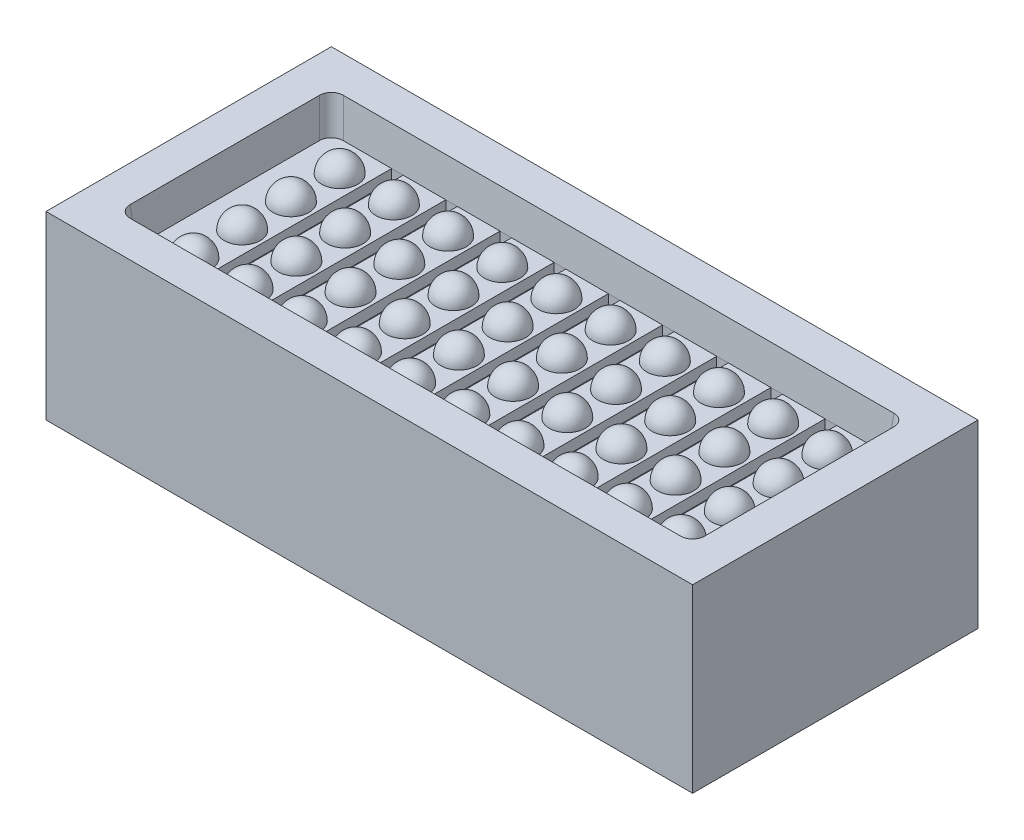
SolidWorks part; units mm, degrees
ref_plane "Front Plane" through (0, 0, 0) normal (0, 0, 1) x (1, 0, 0)
ref_plane "Top Plane" through (0, 0, 0) normal (0, 1, 0) x (1, 0, 0)
ref_plane "Right Plane" through (0, 0, 0) normal (1, 0, 0) x (0, 0, -1)
sketch "Sketch1" plane through (0, 0, 0) normal (0, 1, 0) x (1, 0, 0)
  line L1 (0, 0) -> (-179, 0)
  line L2 (0, 0) -> (0, 79)
  line L3 (0, 79) -> (-179, 79)
  line L4 (-179, 0) -> (-179, 79)
  dimension "D1" = 179
  dimension "D2" = 79
extrude "Boss-Extrude2" add sketch "Sketch1" along normal blind 50
sketch "Sketch2" plane through (0, 50, 0) normal (0, 1, 0) x (1, 0, 0)
  line L0 (0, 79) -> (-179, 79) construction
  line L1 (-169, 69) -> (-10, 69)
  line L2 (-169, 69) -> (-169, 10)
  line L3 (-169, 10) -> (-10, 10)
  line L4 (-10, 69) -> (-10, 10)
  line L5 (-179, 79) -> (-179, 0) construction
  line L6 (0, 0) -> (0, 79) construction
  line L7 (-179, 0) -> (0, 0) construction
  dimension "D1" = 10
  dimension "D2" = 10
  dimension "D3" = 10
  dimension "D4" = 10
extrude "Cut-Extrude1" cut sketch "Sketch2" against normal blind 10 draft 5
fillet "Fillet1" radius 3.3 4 edges at (-10.4374, 45, -10.4374) (-168.5626, 45, -10.4374) (-10.4374, 45, -68.5626) (-168.5626, 45, -68.5626)
sketch "Sketch3" plane through (0, 40, 0) normal (0, 1, 0) x (1, 0, 0)
  line L0 (-157.3488, 64.653) -> (-157.3488, 54.653)
  arc A0 (-157.3488, 54.653) -> (-157.3488, 64.653) centre (-157.3488, 59.653) ccw
  dimension "D1" = 10
revolve "Revolve2" add sketch "Sketch3" angle 360 about L0
pattern_linear "LPattern1" count 10 spacing 15 along (1, 0, 0) of "Revolve2"
pattern_linear "LPattern2" count 4 spacing 13.5 along (0, 0, 1) of "LPattern1", "Revolve2"
sketch "Sketch5" plane through (0, 40, 0) normal (0, 1, 0) x (1, 0, 0)
  line L0 (-152.3488, 59.653) -> (-151.4488, 59.653)
  line L1 (-14.1623, 68.1251) -> (-164.8377, 68.1251) construction
  line L2 (-133.2488, 68.1251) -> (-133.2488, 10.8749)
  line L3 (-164.8377, 10.8749) -> (-14.1623, 10.8749) construction
  line L4 (-148.2488, 68.1251) -> (-151.4488, 68.1251)
  line L5 (-148.2488, 68.1251) -> (-148.2488, 10.8749)
  line L6 (-148.2488, 10.8749) -> (-151.4488, 10.8749)
  line L7 (-151.4488, 68.1251) -> (-151.4488, 10.8749)
  line L8 (-148.2488, 59.653) -> (-147.3488, 59.653)
  line L9 (-136.4488, 68.1251) -> (-136.4488, 10.8749)
  line L10 (-133.2488, 68.1251) -> (-136.4488, 68.1251)
  line L11 (-133.2488, 10.8749) -> (-136.4488, 10.8749)
  line L12 (-118.2488, 68.1251) -> (-118.2488, 10.8749)
  line L13 (-121.4488, 68.1251) -> (-121.4488, 10.8749)
  line L14 (-118.2488, 68.1251) -> (-121.4488, 68.1251)
  line L15 (-118.2488, 10.8749) -> (-121.4488, 10.8749)
  line L16 (-103.2488, 68.1251) -> (-103.2488, 10.8749)
  line L17 (-106.4488, 68.1251) -> (-106.4488, 10.8749)
  line L18 (-103.2488, 68.1251) -> (-106.4488, 68.1251)
  line L19 (-103.2488, 10.8749) -> (-106.4488, 10.8749)
  line L20 (-88.2488, 68.1251) -> (-88.2488, 10.8749)
  line L21 (-91.4488, 68.1251) -> (-91.4488, 10.8749)
  line L22 (-88.2488, 68.1251) -> (-91.4488, 68.1251)
  line L23 (-88.2488, 10.8749) -> (-91.4488, 10.8749)
  line L24 (-73.2488, 68.1251) -> (-73.2488, 10.8749)
  line L25 (-76.4488, 68.1251) -> (-76.4488, 10.8749)
  line L26 (-73.2488, 68.1251) -> (-76.4488, 68.1251)
  line L27 (-73.2488, 10.8749) -> (-76.4488, 10.8749)
  line L28 (-58.2488, 68.1251) -> (-58.2488, 10.8749)
  line L29 (-61.4488, 68.1251) -> (-61.4488, 10.8749)
  line L30 (-58.2488, 68.1251) -> (-61.4488, 68.1251)
  line L31 (-58.2488, 10.8749) -> (-61.4488, 10.8749)
  line L32 (-43.2488, 68.1251) -> (-43.2488, 10.8749)
  line L33 (-46.4488, 68.1251) -> (-46.4488, 10.8749)
  line L34 (-43.2488, 68.1251) -> (-46.4488, 68.1251)
  line L35 (-43.2488, 10.8749) -> (-46.4488, 10.8749)
  line L36 (-28.2488, 68.1251) -> (-28.2488, 10.8749)
  line L37 (-31.4488, 68.1251) -> (-31.4488, 10.8749)
  line L38 (-28.2488, 68.1251) -> (-31.4488, 68.1251)
  line L39 (-28.2488, 10.8749) -> (-31.4488, 10.8749)
  circle A0 centre (-157.3488, 59.653) radius 5 construction
  circle A1 centre (-142.3488, 59.653) radius 5 construction
  point P6 (-149.8488, 68.1251)
  point P7 (-151.4488, 68.1251)
  point P10 (-148.2488, 68.1251)
  point P15 (-134.8488, 68.1251)
  line M42 (-164.8377, 10.8749) -> (-14.1623, 10.8749)
  line M46 (-14.1623, 68.1251) -> (-164.8377, 68.1251)
  dimension "D1" = 5
  dimension "D2" = 1.6
  dimension "D3" = 1.6
  dimension "D4" = 15
  dimension "D5" = 9
extrude "Cut-Extrude3" cut sketch "Sketch5" against normal blind 3 contours L13 L12 M46 M42 | L21 L20 M46 M42 | L25 L24 M46 M42 | L29 L28 M46 M42 | L37 L36 M46 M42 | L9 L11 L2 L10 | L7 L6 L5 L4 | L16 L19 L17 L18 | L33 L35 L32 L34
